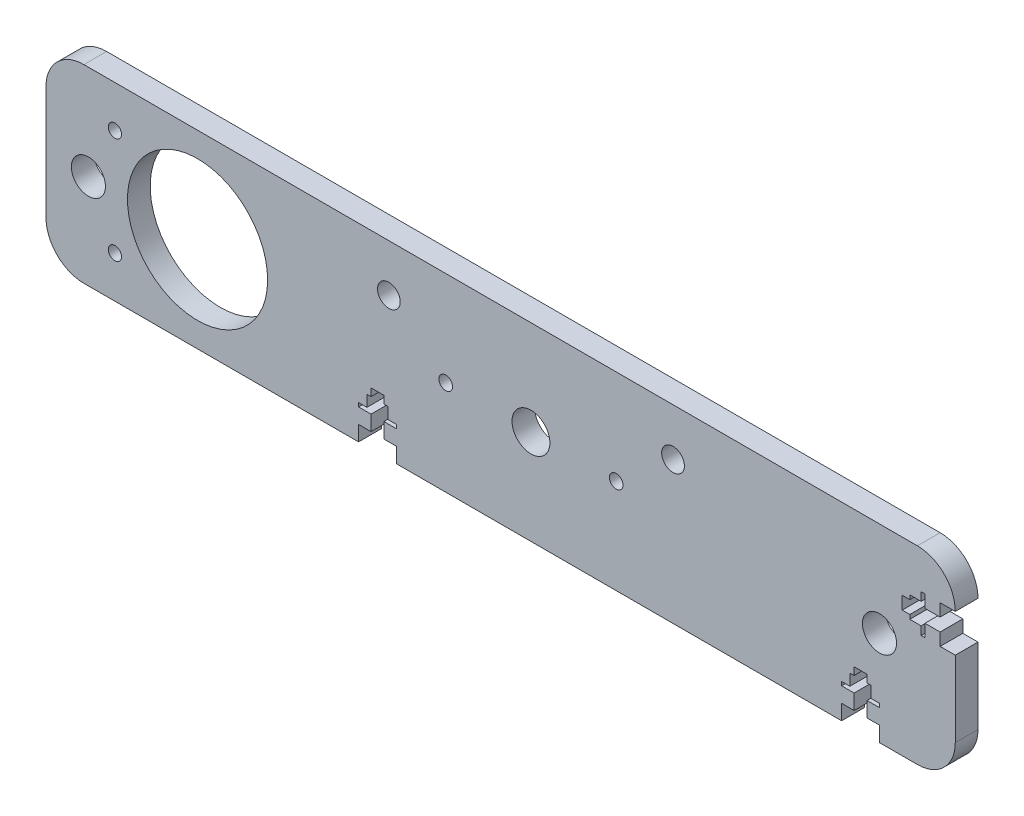
SolidWorks part; units mm, degrees
material "Balsa"
ref_plane "Plano frontal" through (0, 0, 0) normal (0, 0, 1) x (1, 0, 0)
ref_plane "Plano superior" through (0, 0, 0) normal (0, 1, 0) x (1, 0, 0)
ref_plane "Plano direito" through (0, 0, 0) normal (1, 0, 0) x (0, 0, -1)
sketch "Esboço1" plane through (0, 0, 0) normal (0, 0, 1) x (1, 0, 0)
  line L0 (100, -25) -> (100, -21)
  line L1 (-110, -25) -> (-37.5, -25)
  line L2 (-120, -15) -> (-120, 15)
  line L3 (-110, 25) -> (110, 25)
  line L4 (120, 5) -> (120, -15)
  line L5 (-120, -25) -> (120, 25) construction
  line L6 (-120, 25) -> (120, -24.5772) construction
  line L7 (-80, 18.5) -> (-80, 25) construction
  line L8 (8, 25) -> (8, 0) construction
  line L9 (-104.31, 0) -> (-104.31, 1.5)
  line L10 (-29.5, 12.5) -> (45.5, 12.5) construction
  line L11 (-14.5, 0) -> (30.5, 0) construction
  line L12 (100, -21) -> (96.7, -21)
  line L13 (90, -21) -> (90, -25)
  line L14 (-37.5, -25) -> (-37.5, -21)
  line L15 (-37.5, -21) -> (-34.2, -21)
  line L16 (-27.5, -21) -> (-27.5, -25)
  line L17 (-27.5, -25) -> (90, -25)
  line L18 (-32.5, -25) -> (-32.5, -13.0244) construction
  line L19 (-34.2, -21) -> (-34.2, -17)
  line L20 (-34.2, -17) -> (-37.5, -17)
  line L21 (-35.3, -16) -> (-35.3, -13)
  line L22 (-35.3, -13) -> (-34.2, -13)
  line L23 (-37.5, -25) -> (-27.5, -25) construction
  line L24 (-34.2, -13) -> (-34.2, -11)
  line L25 (-34.2, -11) -> (-30.8, -11)
  line L26 (-35.3, -16) -> (-37.5, -16)
  line L27 (-37.5, -16) -> (-37.5, -17)
  line L28 (-27.5, -16) -> (-27.5, -17)
  line L29 (-29.7, -16) -> (-27.5, -16)
  line L30 (-30.8, -13) -> (-30.8, -11)
  line L31 (-29.7, -13) -> (-30.8, -13)
  line L32 (-29.7, -16) -> (-29.7, -13)
  line L33 (-30.8, -17) -> (-27.5, -17)
  line L34 (-30.8, -21) -> (-30.8, -17)
  line L35 (-27.5, -21) -> (-30.8, -21)
  line L36 (100, -16) -> (100, -17)
  line L37 (90, -16) -> (90, -17)
  line L38 (96.7, -17) -> (100, -17)
  line L39 (93.3, -17) -> (90, -17)
  line L40 (96.7, -13) -> (96.7, -11)
  line L41 (97.8, -13) -> (96.7, -13)
  line L42 (93.3, -13) -> (93.3, -11)
  line L43 (93.3, -11) -> (96.7, -11)
  line L44 (93.3, -21) -> (93.3, -17)
  line L45 (95, -25) -> (95, -21) construction
  line L46 (92.2, -16) -> (92.2, -13)
  line L47 (96.7, -21) -> (96.7, -17)
  line L48 (97.8, -16) -> (100, -16)
  line L49 (92.2, -16) -> (90, -16)
  line L50 (92.2, -13) -> (93.3, -13)
  line L51 (97.8, -16) -> (97.8, -13)
  line L52 (93.3, -21) -> (90, -21)
  line L53 (90, -25) -> (100, -25) construction
  line L54 (110, -25) -> (100, -25)
  line L55 (120, 15) -> (116, 15)
  line L56 (116, 15) -> (116, 11.7)
  line L57 (116, 5) -> (120, 5)
  line L58 (111, 15) -> (112, 15)
  line L59 (111, 5) -> (112, 5)
  line L60 (112, 11.7) -> (112, 15)
  line L61 (112, 8.3) -> (112, 5)
  line L62 (108, 11.7) -> (106, 11.7)
  line L63 (108, 12.8) -> (108, 11.7)
  line L64 (108, 8.3) -> (106, 8.3)
  line L65 (106, 8.3) -> (106, 11.7)
  line L66 (116, 8.3) -> (112, 8.3)
  line L67 (111, 7.2) -> (108, 7.2)
  line L68 (116, 11.7) -> (112, 11.7)
  line L69 (111, 12.8) -> (111, 15)
  line L70 (111, 7.2) -> (111, 5)
  line L71 (108, 7.2) -> (108, 8.3)
  line L72 (111, 12.8) -> (108, 12.8)
  line L73 (116, 8.3) -> (116, 5)
  line L74 (-108.81, 0) -> (-76.55, 0) construction
  circle A0 centre (-80, 0) radius 18.5
  circle A1 centre (100, 0) radius 4.5
  arc A2 (120, -15) -> (110, -25) centre (110, -15) cw
  arc A3 (110, 25) -> (120, 15) centre (110, 15) cw
  arc A4 (-120, 15) -> (-110, 25) centre (-110, 15) cw
  arc A5 (-110, -25) -> (-120, -15) centre (-110, -15) cw
  circle A6 centre (8, 0) radius 5
  circle A7 centre (-108.81, 0) radius 4.5
  circle A8 centre (-14.5, 0) radius 1.8
  circle A9 centre (30.5, 0) radius 1.8
  circle A10 centre (-29.5, 12.5) radius 3
  circle A11 centre (45.5, 12.5) radius 3
  circle A12 centre (-101.81, 14) radius 1.75
  circle A13 centre (-101.81, -14) radius 1.75
  point P0 (0, 0)
  point P34 (8, 12.5)
  point P35 (8, 0)
  point P42 (8, 12.5)
  point P60 (-32.5, -25)
  point P67 (-32.5, -11)
  point P84 (94.8463, -8.5)
  point P89 (95, -25)
  point P95 (0, 0)
  point P108 (103.5, 9.8463)
  dimension "D3" = 37
  dimension "D5" = 9
  dimension "D6" = 10
  dimension "D9" = 28.81
  dimension "D10" = 75
  dimension "D11" = 6
  dimension "D12" = 3.6
  dimension "D14" = 10
  dimension "D40" = 3.5
  dimension "D1" = 240
  dimension "D2" = 50
  dimension "D4" = 180
  dimension "D7" = 4
  dimension "D8" = 10
  dimension "D13" = 45
  dimension "D15" = 4
  dimension "D16" = 10
  dimension "D17" = 4
  dimension "D18" = 4
  dimension "D19" = 4
  dimension "D20" = 5.6
  dimension "D21" = 3.4
  dimension "D22" = 2
  dimension "D23" = 1
  dimension "D24" = 10
  dimension "D25" = 4
  dimension "D26" = 5.6
  dimension "D27" = 25
  dimension "D28" = 2
  dimension "D29" = 4
  dimension "D30" = 1
  dimension "D31" = 10
  dimension "D32" = 2
  dimension "D33" = 8
  dimension "D34" = 4
  dimension "D35" = 127.5
  dimension "D36" = 3.4
  dimension "D37" = 25
  dimension "D38" = 7
  dimension "D39" = 14
extrude "Ressalto-extrusão1" add sketch "Esboço1" along normal blind 6
